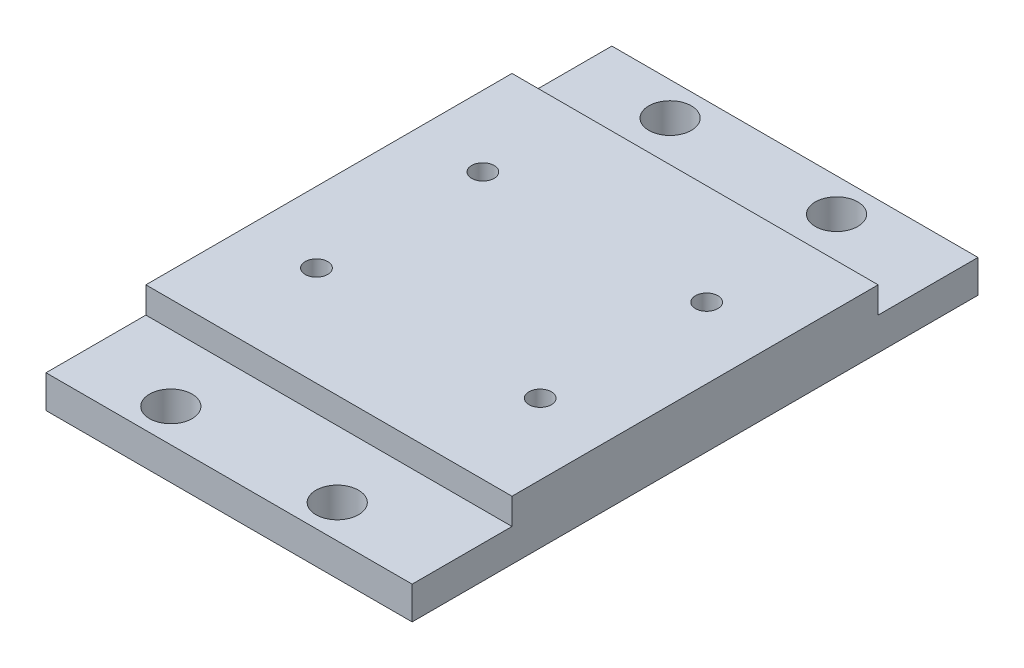
SolidWorks part; units mm, degrees
ref_plane "Front Plane" through (0, 0, 0) normal (0, 0, 1) x (1, 0, 0)
ref_plane "Top Plane" through (0, 0, 0) normal (0, 1, 0) x (1, 0, 0)
ref_plane "Right Plane" through (0, 0, 0) normal (1, 0, 0) x (0, 0, -1)
sketch "Sketch1" plane through (0, 0, 0) normal (0, 1, 0) x (1, 0, 0)
  line L1 (-27.94, -27.94) -> (27.94, -27.94)
  line L2 (-27.94, -27.94) -> (-27.94, 27.94)
  line L3 (-27.94, 27.94) -> (27.94, 27.94)
  line L4 (27.94, -27.94) -> (27.94, 27.94)
  line L5 (-27.94, -27.94) -> (27.94, 27.94) construction
  line L6 (-27.94, 27.94) -> (27.94, -27.94) construction
  point P0 (0, 0)
  dimension "D1" = 55.88
  dimension "D2" = 55.88
extrude "Boss-Extrude1" add sketch "Sketch1" along normal blind 9
hole_wizard "1/4 (0.25) Clearance Dowel Hole1" positions "Sketch2" profile "Sketch3" hole size "1/4" standard "ANSI Inch" end condition through all
sketch "Sketch2" plane through (0, 9, 0) normal (0, 1, 0) x (1, 0, 0)
  line L0 (27.94, 27.94) -> (-27.94, 27.94) construction
  line L1 (27.94, -27.94) -> (27.94, 27.94) construction
  point P0 (-17.1447, -12.7)
  point P2 (-17.1447, 12.7)
  point P5 (17.145, -12.8371)
  point P7 (17.145, 12.5629)
  dimension "D1" = 25.4
  dimension "D2" = 34.29
  dimension "D3" = 25.4
  dimension "D4" = 0
  dimension "D5" = 15.24
  dimension "D6" = 10.795
  dimension "D7" = 0
sketch "Sketch3" plane through (-17.1447, 9, 12.7) normal (1, 0, 0) x (0, 0, 1)
  line L0 (0, 0) -> (0, 9)
  line L1 (0, 9) -> (1.7145, 9)
  line L2 (1.7145, 9) -> (1.7145, 0)
  line L5 (1.7145, 0) -> (0, 0)
  line L11 (0, -6.35) -> (0, 107.95) construction
  dimension "Thru Hole Dia." = 3.429
  dimension "Thru Hole Depth" = 9
sketch "Sketch4" plane through (0, 0, 0) normal (0, -1, 0) x (1, 0, 0)
  line L1 (22.1447, 17.7) -> (-22.1447, 17.7)
  line L2 (22.1447, 17.7) -> (22.1447, -17.7)
  line L3 (22.1447, -17.7) -> (-22.1447, -17.7)
  line L4 (-22.1447, 17.7) -> (-22.1447, -17.7)
  line L5 (22.1447, 17.7) -> (-22.1447, -17.7) construction
  line L6 (22.1447, -17.7) -> (-22.1447, 17.7) construction
  circle A0 centre (-17.1447, -12.7) radius 1.7145 construction
  point P0 (0, 0)
  dimension "D1" = 5
  dimension "D2" = 5
extrude "Cut-Extrude1" cut sketch "Sketch4" against normal offset from surface (4 mm away) 5 up to face at (-17.1447, 9, 14.4145)
sketch "Sketch5" plane through (0, 0, 27.94) normal (0, 0, 1) x (1, 0, 0)
  line L0 (27.94, 9) -> (27.94, 0) construction
  line L1 (-27.94, 0) -> (27.94, 0)
  line L2 (-27.94, 0) -> (-27.94, 5)
  line L3 (-27.94, 5) -> (27.94, 5)
  line L4 (27.94, 0) -> (27.94, 5)
  line L5 (-27.94, 0) -> (27.94, 0) construction
  dimension "D1" = 5
extrude "Boss-Extrude2" add sketch "Sketch5" along normal blind 15.24
sketch "Sketch6" plane through (0, 0, -27.94) normal (0, 0, -1) x (-1, 0, 0)
  line L0 (27.94, 9) -> (27.94, 0) construction
  line L1 (-27.94, 0) -> (27.94, 0)
  line L2 (-27.94, 0) -> (-27.94, 5)
  line L3 (-27.94, 5) -> (27.94, 5)
  line L4 (27.94, 0) -> (27.94, 5)
  line L5 (-27.94, 0) -> (27.94, 0) construction
  dimension "D1" = 5
extrude "Boss-Extrude3" add sketch "Sketch6" along normal blind 15.24
hole_wizard "1/4 (0.25) Clearance Dowel Hole2" positions "Sketch7" profile "Sketch8" hole size "1/4" standard "ANSI Inch" end condition through all
sketch "Sketch7" plane through (0, 5, 0) normal (0, 1, 0) x (1, 0, 0)
  line L0 (27.94, -43.18) -> (-27.94, -43.18) construction
  line L1 (-27.94, -43.18) -> (-27.94, -27.94) construction
  point P0 (11.43, 38.1)
  point P2 (-13.97, 38.1)
  point P5 (-13.97, -38.1)
  point P7 (11.43, -38.1)
  dimension "D1" = 25.4
  dimension "D2" = 76.2
  dimension "D3" = 76.2
  dimension "D4" = 5.08
  dimension "D5" = 13.97
sketch "Sketch8" plane through (11.43, 5, -38.1) normal (1, 0, 0) x (0, 0, 1)
  line L0 (0, 0) -> (0, 5)
  line L1 (0, 5) -> (3.25, 5)
  line L2 (3.25, 5) -> (3.25, 0)
  line L5 (3.25, 0) -> (0, 0)
  line L11 (0, -6.35) -> (0, 107.95) construction
  dimension "Thru Hole Dia." = 6.5
  dimension "Thru Hole Depth" = 5
